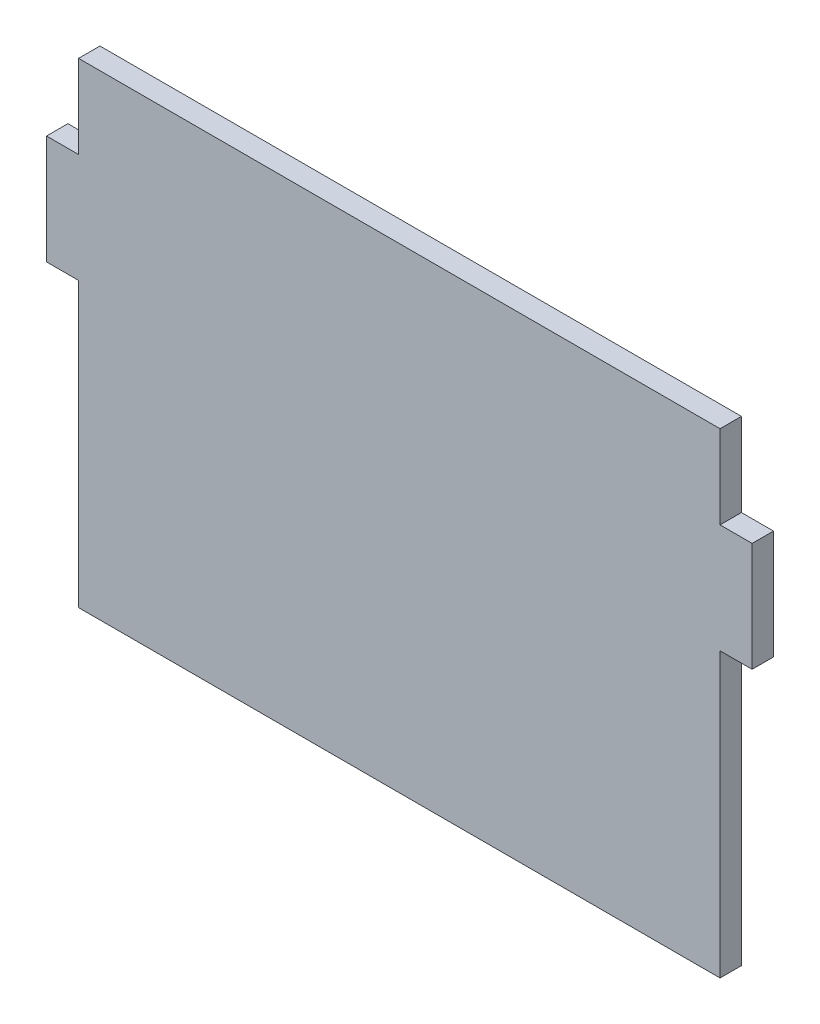
SolidWorks part; units mm, degrees
ref_plane "Ön Düzlem" through (0, 0, 0) normal (0, 0, 1) x (1, 0, 0)
ref_plane "Üst Düzlem" through (0, 0, 0) normal (0, 1, 0) x (1, 0, 0)
ref_plane "Sağ Düzlem" through (0, 0, 0) normal (1, 0, 0) x (0, 0, -1)
sketch "Çizim1" plane through (0, 0, 0) normal (0, 0, 1) x (1, 0, 0)
  line L0 (-150, -111.235) -> (-150, 21.285)
  line L1 (-150, -111.235) -> (150, -111.235) construction
  line L2 (-150, -111.235) -> (-150, 111.235) construction
  line L3 (-150, 111.235) -> (150, 111.235) construction
  line L4 (150, -111.235) -> (150, 111.235) construction
  line L5 (-150, -111.235) -> (150, 111.235) construction
  line L6 (-150, 111.235) -> (150, -111.235) construction
  line L7 (-150, 21.285) -> (-165, 21.285)
  line L8 (-165, 21.285) -> (-165, 72.285)
  line L9 (-165, 72.285) -> (-150, 72.285)
  line L10 (-150, 72.285) -> (-150, 111.235)
  line L11 (-150, 111.235) -> (150, 111.235)
  line L12 (150, 111.235) -> (150, 72.285)
  line L13 (150, 72.285) -> (165, 72.285)
  line L14 (165, 72.285) -> (165, 21.285)
  line L15 (165, 21.285) -> (150, 21.285)
  line L16 (150, 21.285) -> (150, -111.235)
  line L17 (150, -111.235) -> (-150, -111.235)
  point P0 (0, 0)
  dimension "D1" = 222.47
  dimension "D2" = 300
  dimension "D3" = 38.95
  dimension "D4" = 51
  dimension "D5" = 15
extrude "Yükseklik-Ekstrüzyon1" add sketch "Çizim1" along normal blind 10
